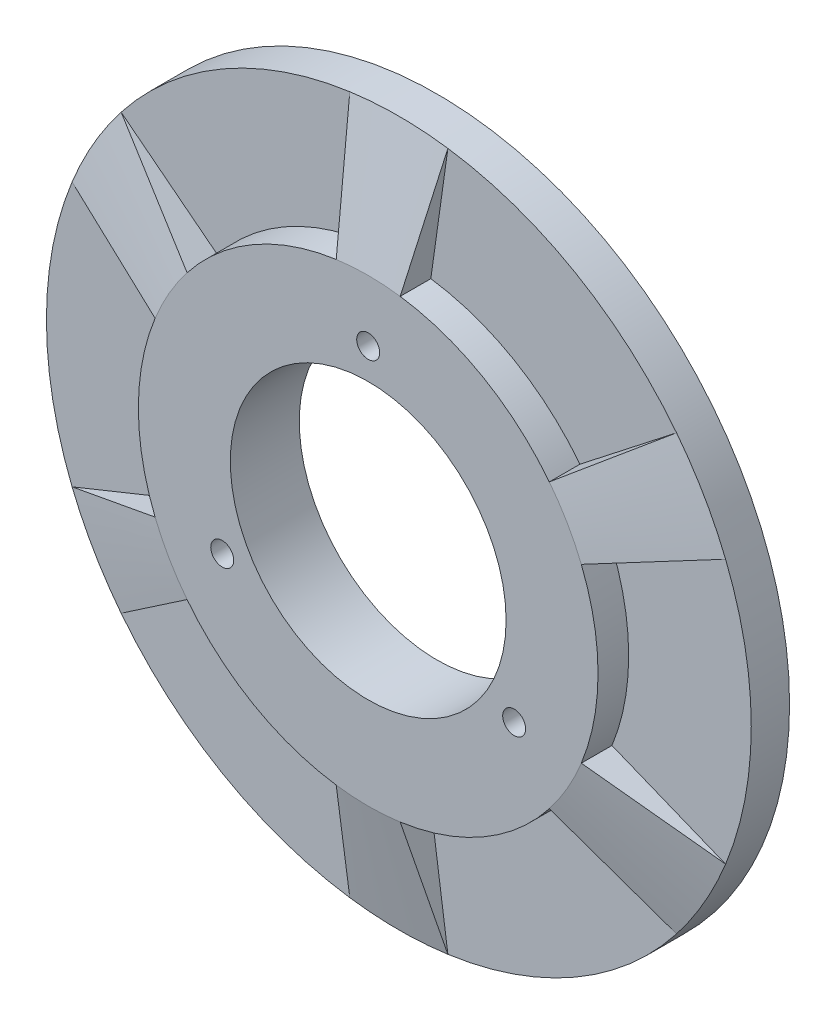
SolidWorks part; units mm, degrees
material "AISI 316 Stainless Steel Sheet (SS)"
ref_plane "Front Plane" through (0, 0, 0) normal (0, 0, 1) x (1, 0, 0)
ref_plane "Top Plane" through (0, 0, 0) normal (0, 1, 0) x (1, 0, 0)
ref_plane "Right Plane" through (0, 0, 0) normal (1, 0, 0) x (0, 0, -1)
sketch "Sketch2" plane through (0, 0, 0) normal (0, 0, 1) x (1, 0, 0)
  circle A0 centre (0, 0) radius 46
  circle A2 centre (0, 0) radius 18
  point P13 (0, 0)
  dimension "D1" = 36
  dimension "D2" = 92
extrude "Boss-Extrude2" add sketch "Sketch2" along normal blind 5
sketch "Sketch4" plane through (0, 0, 5) normal (0, 0, 1) x (1, 0, 0)
  circle A0 centre (0, 0) radius 30
  circle A1 centre (0, 0) radius 18
  dimension "D1" = 60
extrude "Boss-Extrude3" add sketch "Sketch4" along normal blind 4
sketch "Sketch5" plane through (0, 0, 0) normal (0, 0, -1) x (-1, 0, 0)
  circle A0 centre (0, 0) radius 22 construction
  circle A1 centre (0, 22) radius 1.5
  circle A2 centre (19.0526, -11) radius 1.5
  circle A3 centre (-19.0526, -11) radius 1.5
  point P11 (0, 0)
  dimension "D1" = 44
  dimension "D2" = 3
  dimension "D3" = 3
extrude "Cut-Extrude1" cut sketch "Sketch5" against normal through all both and the other way through all
sketch "Sketch6" plane through (0, 0, 0) normal (1, 0, 0) x (0, 0, -1)
  line L0 (-5, 30) -> (-9, 30)
  line L1 (-9, 30) -> (-5, 46)
  line L2 (-5, 46) -> (-5, 30)
  line L3 (0, 0) -> (32.6688, 0) construction
revolve "Revolve1" add sketch "Sketch6" angle 16 mid plane about L3
pattern_circular "CirPattern1" count 6 over 360 about axis through (0, 0, 0) along (0, 0, 1) of "Revolve1"
